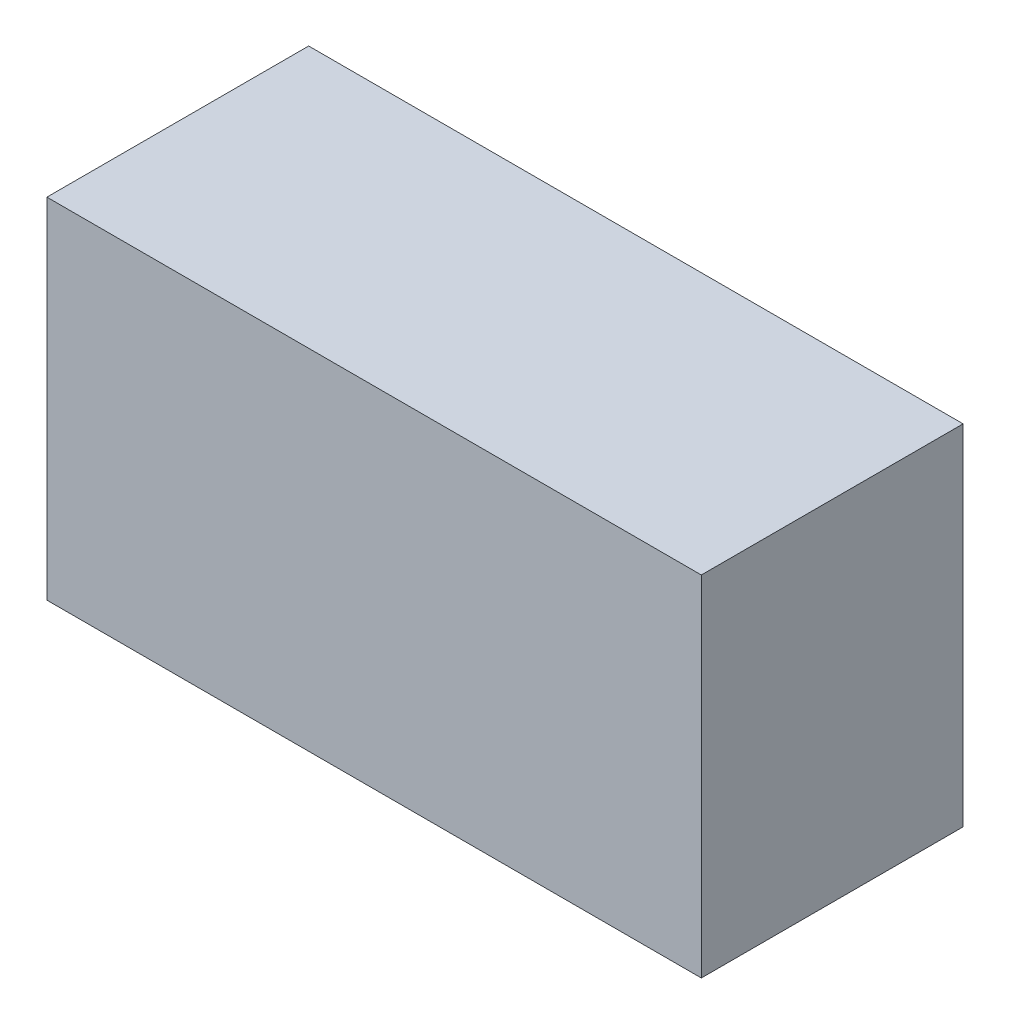
SolidWorks part; units mm, degrees
ref_plane "Front Plane" through (0, 0, 0) normal (0, 0, 1) x (1, 0, 0)
ref_plane "Top Plane" through (0, 0, 0) normal (0, 1, 0) x (1, 0, 0)
ref_plane "Right Plane" through (0, 0, 0) normal (1, 0, 0) x (0, 0, -1)
sketch "Sketch1" plane through (0, 0, 0) normal (0, 0, 1) x (1, 0, 0)
  line L1 (0, 0) -> (150, 0)
  line L2 (0, 0) -> (0, 80)
  line L3 (0, 80) -> (150, 80)
  line L4 (150, 0) -> (150, 80)
  dimension "D1" = 150
  dimension "D2" = 80
extrude "Boss-Extrude1" add sketch "Sketch1" along normal blind 60
shell "Shell5" thickness 3
sketch "Sketch2" plane through (0, 0, 0) normal (1, 0, 0) x (0, 0, -1)
  line L9 (0, 0) -> (-60, 0)
  line L10 (0, 0) -> (0, 80)
  line L11 (0, 80) -> (-60, 80)
  line L12 (-60, 0) -> (-60, 80)
extrude "Boss-Extrude2" add sketch "Sketch2" along normal blind 3
sketch "Sketch3" plane through (0, 0, 0) normal (0, 1, 0) x (1, 0, 0)
  circle A0 centre (113.2984, -40) radius 16
  circle A1 centre (139.1129, -25.7369) radius 1.5
  circle A2 centre (123.2575, -11.9244) radius 1.5
  circle A3 centre (102.2294, -11.9244) radius 1.5
  circle A4 centre (86.374, -25.7369) radius 1.5
  circle A5 centre (41.4183, -40) radius 1.5
  dimension "D2" = 3
  dimension "D3" = 32
  dimension "D4" = 3
  dimension "D1" = 4
extrude "Cut-Extrude1" cut sketch "Sketch3" along normal up to next
sketch "Sketch4" plane through (0, 0, 0) normal (0, 1, 0) x (1, 0, 0)
  text T0 "DISENGAGED" font "Century Gothic" height in points 8
  text T1 "1\r\n"
  text T2 "2"
  text T3 "3"
  text T4 "DEAD MANS HANDLE"
extrude "Cut-Extrude2" cut sketch "Sketch4" along normal blind 1
